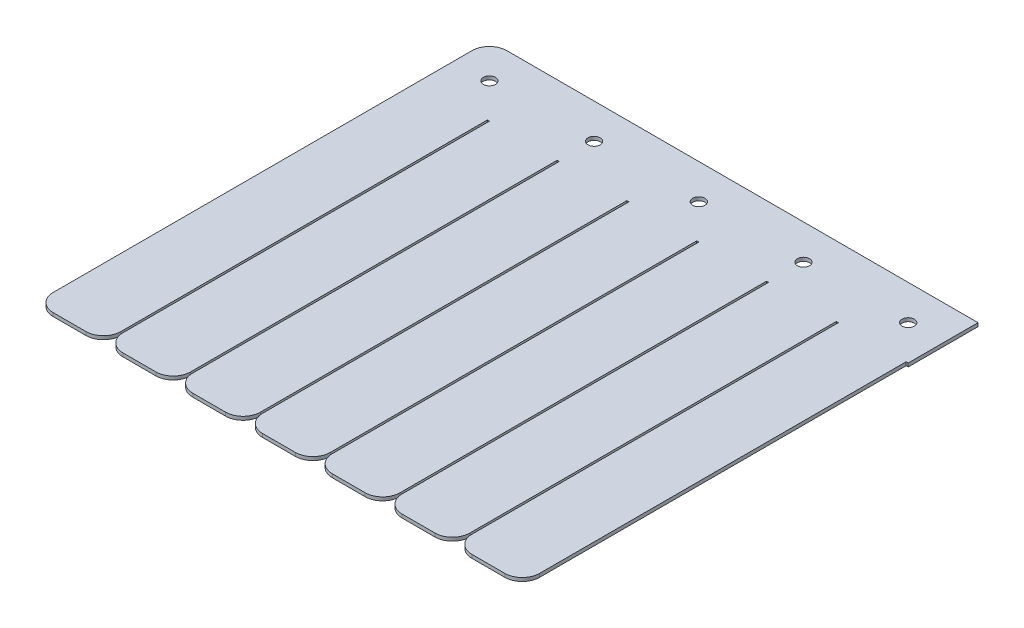
SolidWorks part; units mm, degrees
ref_plane "Front Plane" through (0, 0, 0) normal (0, 0, 1) x (1, 0, 0)
ref_plane "Top Plane" through (0, 0, 0) normal (0, 1, 0) x (1, 0, 0)
ref_plane "Right Plane" through (0, 0, 0) normal (1, 0, 0) x (0, 0, -1)
sketch "Sketch1" plane through (0, 0, 0) normal (0, 1, 0) x (1, 0, 0)
  line L0 (20, 0) -> (20, -105)
  line L1 (0, 0) -> (140, 0)
  line L2 (0, 0) -> (0, 15)
  line L3 (5, 20) -> (140, 20)
  line L4 (140, 0) -> (140, 20)
  line L5 (0, 0) -> (19.4, 0)
  line L6 (0, 0) -> (0, -105)
  line L7 (5, -110) -> (14.4, -110)
  line L8 (19.4, 0) -> (19.4, -105)
  line L9 (20, 0) -> (39.4, 0)
  line L10 (39.4, 0) -> (39.4, -105)
  line L11 (25, -110) -> (34.4, -110)
  line L12 (40, 0) -> (40, -105)
  line L13 (40, 0) -> (59.4, 0)
  line L14 (59.4, 0) -> (59.4, -105)
  line L15 (45, -110) -> (54.4, -110)
  line L16 (60, 0) -> (60, -105)
  line L17 (60, 0) -> (79.4, 0)
  line L18 (79.4, 0) -> (79.4, -105)
  line L19 (65, -110) -> (74.4, -110)
  line L20 (80, 0) -> (80, -105)
  line L21 (80, 0) -> (99.4, 0)
  line L22 (99.4, 0) -> (99.4, -105)
  line L23 (85, -110) -> (94.4, -110)
  line L24 (100, 0) -> (100, -105)
  line L25 (100, 0) -> (119.4, 0)
  line L26 (119.4, 0) -> (119.4, -105)
  line L27 (105, -110) -> (114.4, -110)
  line L28 (120, 0) -> (120, -105)
  line L29 (120, 0) -> (139.4, 0)
  line L30 (139.4, 0) -> (139.4, -105)
  line L31 (125, -110) -> (134.4, -110)
  arc A0 (0, 15) -> (5, 20) centre (5, 15) cw
  arc A1 (14.4, -110) -> (19.4, -105) centre (14.4, -105) ccw
  arc A2 (0, -105) -> (5, -110) centre (5, -105) ccw
  arc A3 (20, -105) -> (25, -110) centre (25, -105) ccw
  arc A4 (34.4, -110) -> (39.4, -105) centre (34.4, -105) ccw
  arc A5 (40, -105) -> (45, -110) centre (45, -105) ccw
  arc A6 (54.4, -110) -> (59.4, -105) centre (54.4, -105) ccw
  arc A7 (60, -105) -> (65, -110) centre (65, -105) ccw
  arc A8 (74.4, -110) -> (79.4, -105) centre (74.4, -105) ccw
  arc A9 (80, -105) -> (85, -110) centre (85, -105) ccw
  arc A10 (94.4, -110) -> (99.4, -105) centre (94.4, -105) ccw
  arc A11 (100, -105) -> (105, -110) centre (105, -105) ccw
  arc A12 (114.4, -110) -> (119.4, -105) centre (114.4, -105) ccw
  arc A13 (120, -105) -> (125, -110) centre (125, -105) ccw
  arc A14 (134.4, -110) -> (139.4, -105) centre (134.4, -105) ccw
  point P10 (0, 20)
  point P13 (19.4, -110)
  point P16 (0, -110)
  dimension "D5" = 5
  dimension "D1" = 20
  dimension "D2" = 140
  dimension "D3" = 110
  dimension "D4" = 19.4
  dimension "D7" = 0.6
  dimension "D6" = 7
extrude "Boss-Extrude1" add sketch "Sketch1" along normal blind 1 contours A0 L2 L1 L4 L3 | L6 A2 L7 A1 L8 L1 | L11 A4 L10 L1 L0 A3 | L15 A6 L14 L1 L12 A5 | L19 A8 L18 L1 L16 A7 | L23 A10 L22 L1 L20 A9 | L27 A12 L26 L1 L24 A11 | L31 A14 L30 L1 L28 A13
sketch "Sketch2" plane through (0, 1, 0) normal (0, 1, 0) x (1, 0, 0)
  line L0 (140, 10) -> (0, 10) construction
  line L2 (140, 0) -> (140, 20) construction
  line L3 (0, -105) -> (0, 15) construction
  circle A0 centre (10, 10) radius 1.75
  circle A1 centre (40, 10) radius 1.75
  circle A2 centre (70, 10) radius 1.75
  circle A3 centre (100, 10) radius 1.75
  circle A4 centre (130, 10) radius 1.75
  dimension "D1" = 10
  dimension "D2" = 3.5
  dimension "D4" = 30
  dimension "D3" = 5
extrude "Cut-Extrude1" cut sketch "Sketch2" against normal up to next
